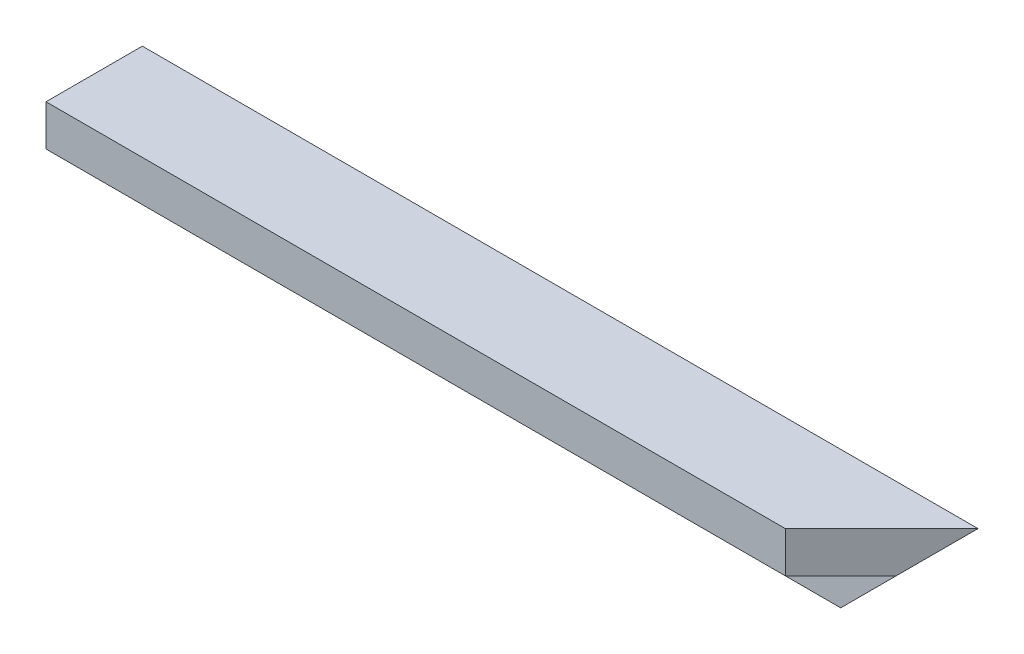
SolidWorks part; units mm, degrees
ref_plane "Plan de face" through (0, 0, 0) normal (0, 0, 1) x (1, 0, 0)
ref_plane "Plan de dessus" through (0, 0, 0) normal (0, 1, 0) x (1, 0, 0)
ref_plane "Plan de droite" through (0, 0, 0) normal (1, 0, 0) x (0, 0, -1)
sketch "Esquisse1" plane through (0, 0, 0) normal (1, 0, 0) x (0, 0, -1)
  line L0 (0, 0) -> (-40, 0)
  line L1 (-40, 0) -> (-40, -17)
  line L2 (-40, -17) -> (-17, -17)
  line L3 (-17, -17) -> (-17, -40)
  line L4 (-17, -40) -> (0, -40)
  line L5 (0, -40) -> (0, 0)
  dimension "D1" = 40
  dimension "D2" = 17
extrude "Boss.-Extru.1" add sketch "Esquisse1" along normal up to vertex (222 mm away) from vertex at -125
sketch "Esquisse2" plane through (0, 0, 0) normal (0, 1, 0) x (1, 0, 0)
  line L0 (222, 0) -> (182, -40)
  line L1 (222, -40) -> (-125, -40) construction
  line L2 (182, -40) -> (222, -40)
  line L3 (222, -40) -> (222, 0)
extrude "Enlèv. mat.-Extru.1" cut sketch "Esquisse2" against normal through all
sketch "Esquisse3" plane through (0, 0, 0) normal (0, 0, -1) x (-1, 0, 0)
  line L0 (-222, 0) -> (-182, -40)
  line L1 (-222, -40) -> (125, -40) construction
  line L2 (-182, -40) -> (-222, -40)
  line L3 (-222, -40) -> (-222, 0)
extrude "Enlèv. mat.-Extru.2" cut sketch "Esquisse3" against normal through all
